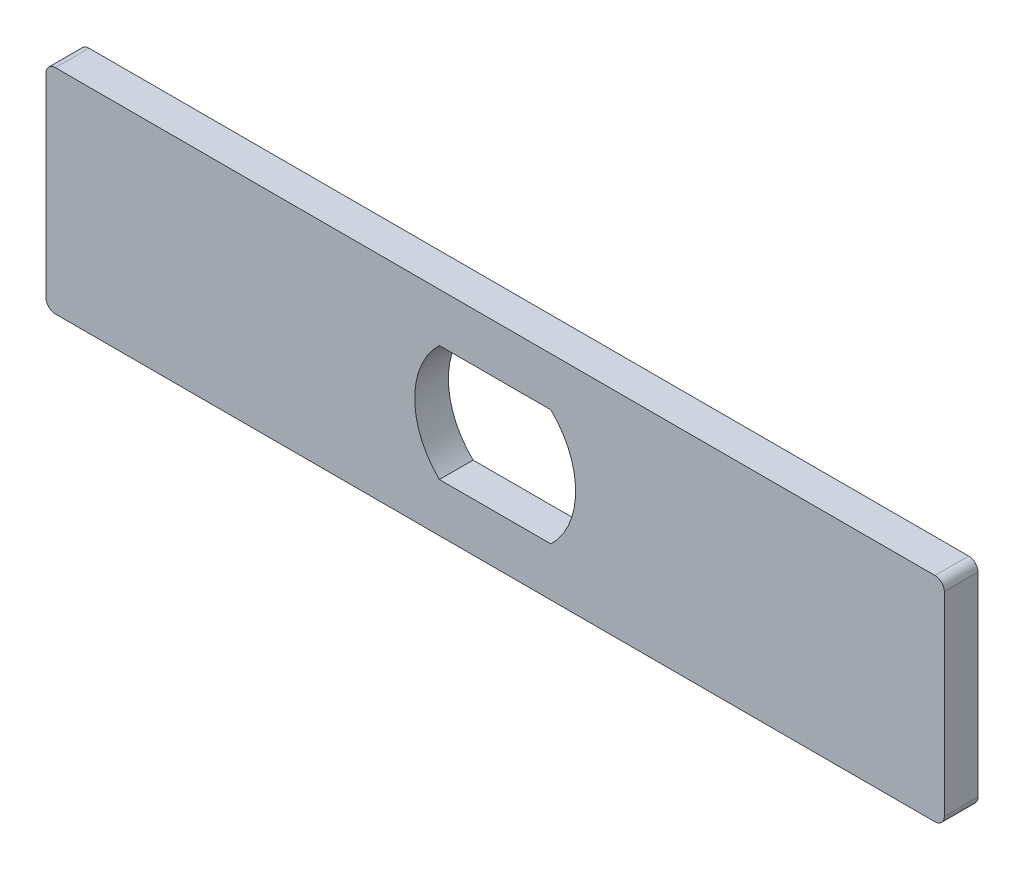
SolidWorks part; units mm, degrees
ref_plane "Front Plane" through (0, 0, 0) normal (0, 0, 1) x (1, 0, 0)
ref_plane "Top Plane" through (0, 0, 0) normal (0, 1, 0) x (1, 0, 0)
ref_plane "Right Plane" through (0, 0, 0) normal (1, 0, 0) x (0, 0, -1)
sketch "Sketch1" plane through (0, 0, 0) normal (0, 0, 1) x (1, 0, 0)
  line L2 (-7.6256, -7.822) -> (7.5079, -7.822)
  line L3 (-0.0589, -14.4239) -> (60.9011, -14.4239)
  line L4 (-0.0589, 14.5321) -> (60.9011, 14.5321)
  line L5 (-7.6256, 7.9303) -> (7.5079, 7.9303)
  line L6 (-0.0589, 14.5321) -> (60.9011, 14.5321)
  line L7 (-0.0589, 14.5321) -> (-61.0189, 14.5321)
  line L8 (-0.0589, -14.4239) -> (60.9011, -14.4239)
  line L9 (-0.0589, -14.4239) -> (-61.0189, -14.4239)
  line L10 (-61.0189, -14.4239) -> (-61.0189, 14.5321)
  line L11 (60.9011, 14.5321) -> (60.9011, -14.4239)
  arc A2 (7.5079, -7.822) -> (7.5079, 7.9303) centre (-0.0589, 0.0541) ccw
  arc A3 (-7.6256, 7.9303) -> (-7.6256, -7.822) centre (-0.0589, 0.0541) ccw
extrude "Boss-Extrude1" add sketch "Sketch1" along normal blind 4.572 contours L11 L4 L7 L10 L9 L3 A3 L5 A2 L2
fillet "Fillet3" radius 1.27 1 edges at (-61.0189, 14.5321, 2.286)
fillet "Fillet4" radius 1.27 1 edges at (-61.0189, -14.4239, 2.286)
fillet "Fillet5" radius 1.27 1 edges at (60.9011, -14.4239, 2.286)
fillet "Fillet6" radius 1.27 1 edges at (60.9011, 14.5321, 2.286)
